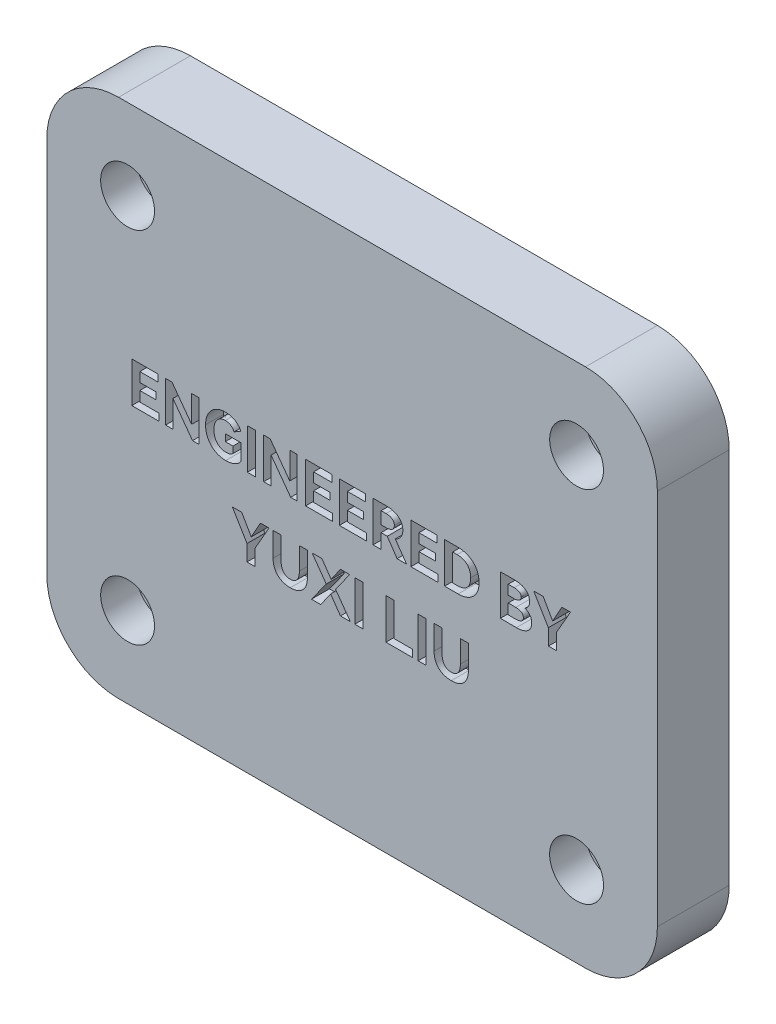
SolidWorks part; units mm, degrees
material "PETG-CF"
ref_plane "前视基准面" through (0, 0, 0) normal (0, 0, 1) x (1, 0, 0)
ref_plane "上视基准面" through (0, 0, 0) normal (0, 1, 0) x (1, 0, 0)
ref_plane "右视基准面" through (0, 0, 0) normal (1, 0, 0) x (0, 0, -1)
other "Configuration Table"
sketch "Sketch1" plane through (0, 0, 0) normal (0, 0, 1) x (1, 0, 0)
  line L1 (0, 0) -> (68, 0)
  line L2 (0, 0) -> (0, 58)
  line L3 (0, 58) -> (68, 58)
  line L4 (68, 0) -> (68, 58)
  dimension "D1" = 58
  dimension "D2" = 68
extrude "Boss-Extrude1" add sketch "Sketch1" along normal blind 8
sketch "Sketch2" plane through (0, 0, 8) normal (0, 0, 1) x (1, 0, 0)
  line L1 (9, 49) -> (59, 49) construction
  line L2 (9, 49) -> (9, 9) construction
  line L3 (9, 9) -> (59, 9) construction
  line L4 (59, 49) -> (59, 9) construction
  line L5 (68, 58) -> (0, 58) construction
  line L6 (68, 0) -> (68, 58) construction
  line L7 (9, 29) -> (59, 29) construction
  line L8 (34, 9) -> (34, 49) construction
  circle A0 centre (9, 49) radius 1.6
  circle A1 centre (59, 49) radius 1.6
  circle A2 centre (59, 9) radius 1.6
  circle A3 centre (9, 9) radius 1.6
  point P6 (34, 58)
  point P7 (34, 49)
  point P8 (68, 29)
  point P11 (59, 29)
  dimension "D3" = 3.2
  dimension "D1" = 40
  dimension "D2" = 50
extrude "Cut-Extrude1" cut sketch "Sketch2" against normal through all
sketch "Sketch3" plane through (0, 0, 8) normal (0, 0, 1) x (1, 0, 0)
  line L0 (34, 49) -> (34, 9) construction
  line L1 (9, 9) -> (59, 9) construction
  line L2 (9, 29) -> (59, 29) construction
  line L3 (9, 49) -> (9, 9) construction
  circle A0 centre (9, 49) radius 3
  circle A1 centre (59, 49) radius 3
  circle A2 centre (59, 9) radius 3
  circle A3 centre (9, 9) radius 3
  dimension "D1" = 6
extrude "Cut-Extrude2" cut sketch "Sketch3" against normal blind 4
fillet "Fillet1" radius 8 4 edges at (0, 0, 4) (68, 0, 4) (68, 58, 4) (0, 58, 4)
sketch "Sketch4" plane through (0, 0, 8) normal (0, 0, 1) x (1, 0, 0)
  text T0 "ENGINEERED BY \r\nYUXI LIU" font "HarmonyOS Sans SC" height 4.5
extrude "Cut-Extrude3" cut sketch "Sketch4" against normal blind 2
